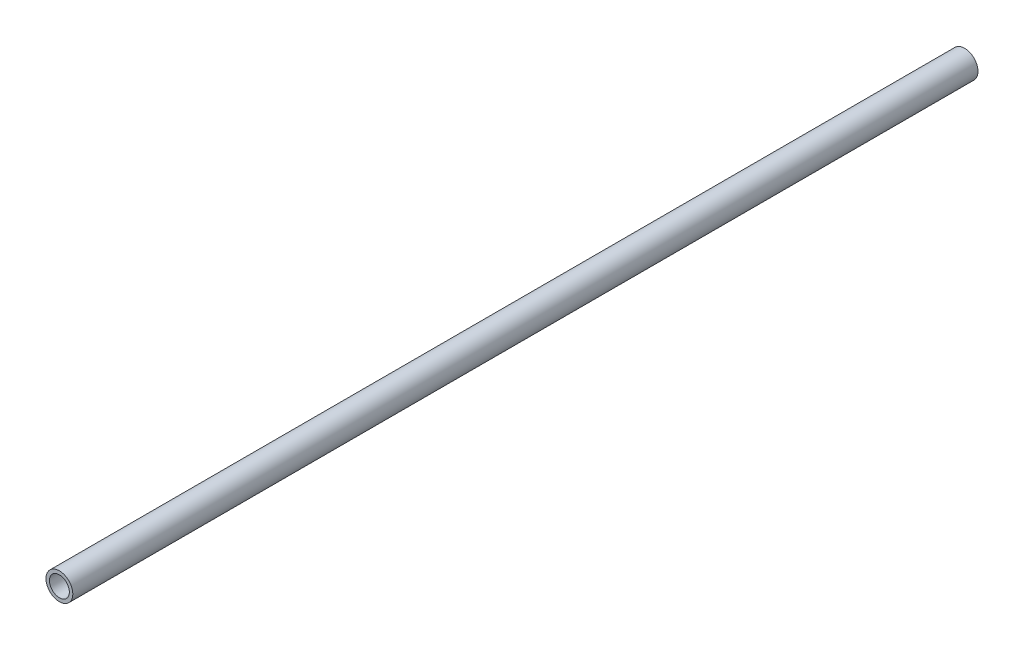
SolidWorks part; units mm, degrees
ref_plane "Front Plane" through (0, 0, 0) normal (0, 0, 1) x (1, 0, 0)
ref_plane "Top Plane" through (0, 0, 0) normal (0, 1, 0) x (1, 0, 0)
ref_plane "Right Plane" through (0, 0, 0) normal (1, 0, 0) x (0, 0, -1)
sketch "Sketch1" plane through (0, 0, 0) normal (0, 0, 1) x (1, 0, 0)
  circle A0 centre (0, 0) radius 10.668
  dimension "Pipe OD" = 21.336
extrude "Extrude-Thin1" add sketch "Sketch1" along normal mid plane 720 thin thin type one direction reverse wall 2.7686
